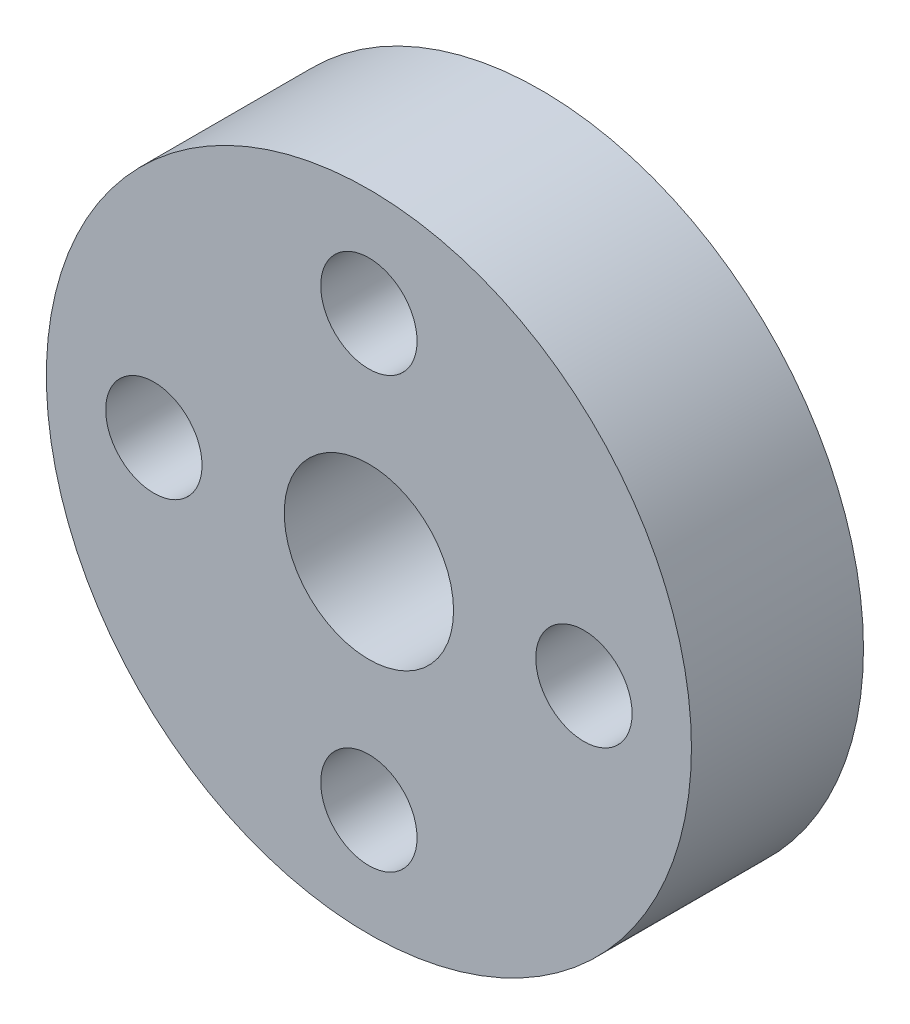
SolidWorks part; units mm, degrees
ref_plane "Front Plane" through (0, 0, 0) normal (0, 0, 1) x (1, 0, 0)
ref_plane "Top Plane" through (0, 0, 0) normal (0, 1, 0) x (1, 0, 0)
ref_plane "Right Plane" through (0, 0, 0) normal (1, 0, 0) x (0, 0, -1)
sketch "Sketch1" plane through (0, 0, 0) normal (0, 0, 1) x (1, 0, 0)
  circle A0 centre (-49.267, 24.9216) radius 9.525
  circle A1 centre (-49.267, 24.9216) radius 2.5
  circle A2 centre (-49.267, 31.2716) radius 1.4225
  circle A3 centre (-42.917, 24.9216) radius 1.4225
  circle A4 centre (-49.267, 18.5716) radius 1.4225
  circle A5 centre (-55.617, 24.9216) radius 1.4225
  dimension "D1" = 19.05
  dimension "D2" = 5
  dimension "D3" = 2.845
  dimension "D4" = 6.35
  dimension "D5" = 6.35
  dimension "D6" = 6.35
  dimension "D7" = 6.35
extrude "Boss-Extrude1" add sketch "Sketch1" along normal blind 5.08
